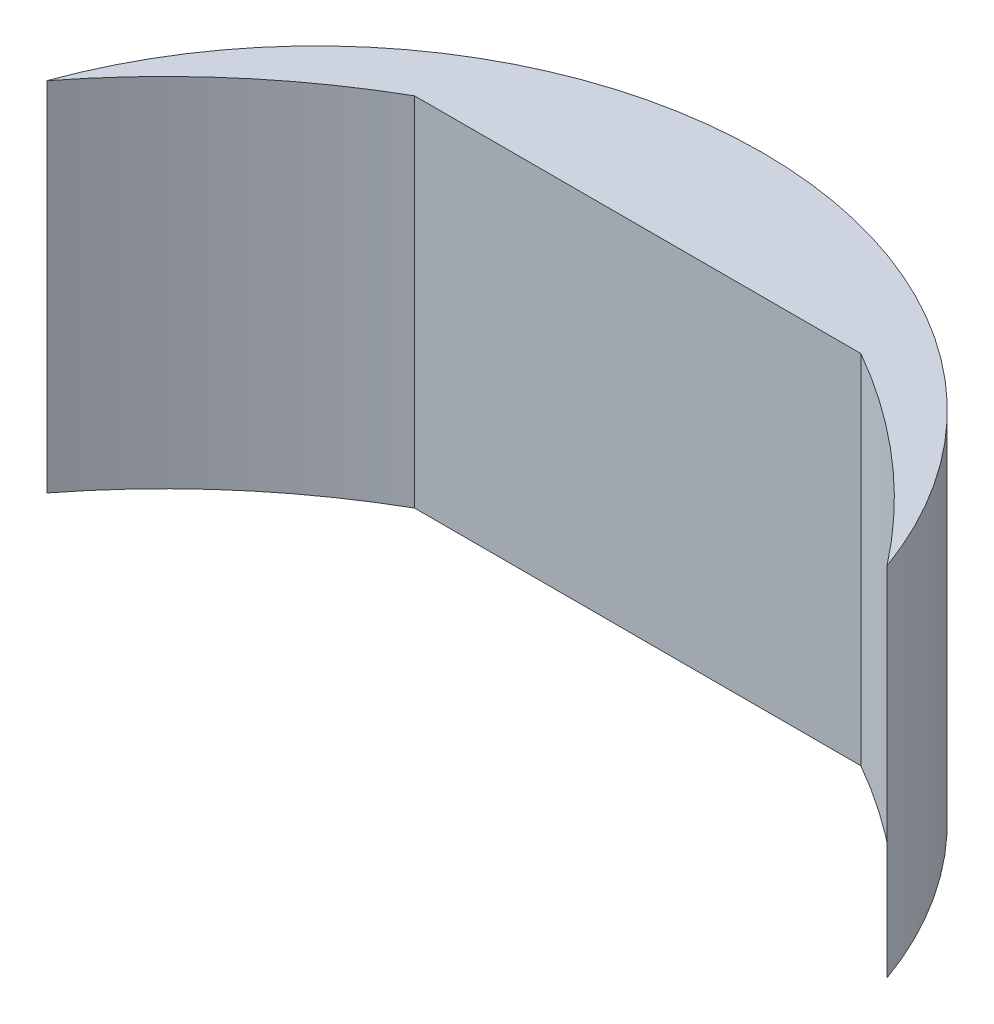
SolidWorks part; units mm, degrees
ref_plane "Front Plane" through (0, 0, 0) normal (0, 0, 1) x (1, 0, 0)
ref_plane "Top Plane" through (0, 0, 0) normal (0, 1, 0) x (1, 0, 0)
ref_plane "Right Plane" through (0, 0, 0) normal (1, 0, 0) x (0, 0, -1)
sketch "Sketch5" plane through (0, 0, 0) normal (0, 1, 0) x (1, 0, 0)
  line L0 (0, 0) -> (127, 0)
  line L1 (63.5, 0) -> (63.5, -18.9564) construction
  arc A0 (127, 0) -> (183.0312, -48.5811) centre (32.6077, -165.4701) cw
  arc A1 (0, 0) -> (-56.0312, -48.5811) centre (94.3923, -165.4701) ccw
  arc A2 (-56.0312, -48.5811) -> (183.0312, -48.5811) centre (63.5, -91.4914) cw
  point P10 (195.7312, -48.5811)
  dimension "D1" = 127
  dimension "D2" = 127
extrude "Boss-Extrude7" add sketch "Sketch5" along normal blind 101.6
